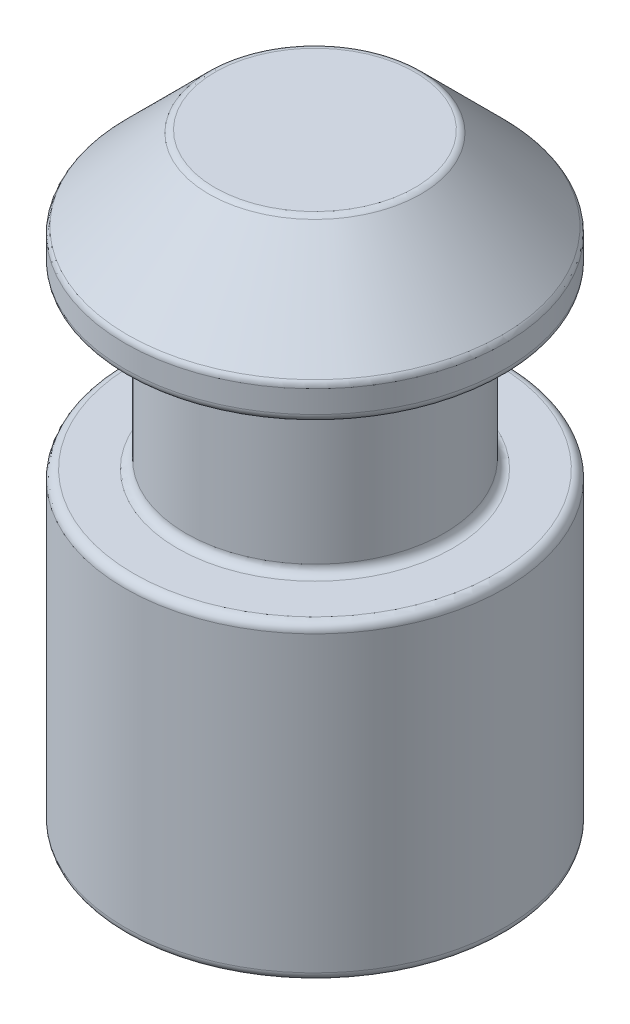
SolidWorks part; units mm, degrees
ref_plane "Front Plane" through (0, 0, 0) normal (0, 0, 1) x (1, 0, 0)
ref_plane "Top Plane" through (0, 0, 0) normal (0, 1, 0) x (1, 0, 0)
ref_plane "Right Plane" through (0, 0, 0) normal (1, 0, 0) x (0, 0, -1)
sketch "Sketch1" plane through (0, 0, 0) normal (0, 1, 0) x (1, 0, 0)
  circle A0 centre (0, 0) radius 1.1
  dimension "D1" = 2.2
extrude "Boss-Extrude1" add sketch "Sketch1" along normal blind 3.5
chamfer "Chamfer1" distance 0.5 angle 45 1 edges at (0, 3.5, 1.1)
sketch "Sketch2" plane through (0, 3.5, 0) normal (0, 1, 0) x (1, 0, 0)
  circle A0 centre (0, 0) radius 0.7471
  circle A1 centre (0, 0) radius 1.3961
extrude "Cut-Extrude1" cut sketch "Sketch2" against normal blind 1 from offset 0.7 offset against normal yes
fillet "Fillet1" radius 0.05 7 edges at (0, 3, 1.1) (0, 3.5, 0.6) (0, 0, 1.1) (0, 1.8, 1.1) (0, 2.8, 1.1) (0, 1.8, 0.7471) (0, 2.8, 0.7471)
